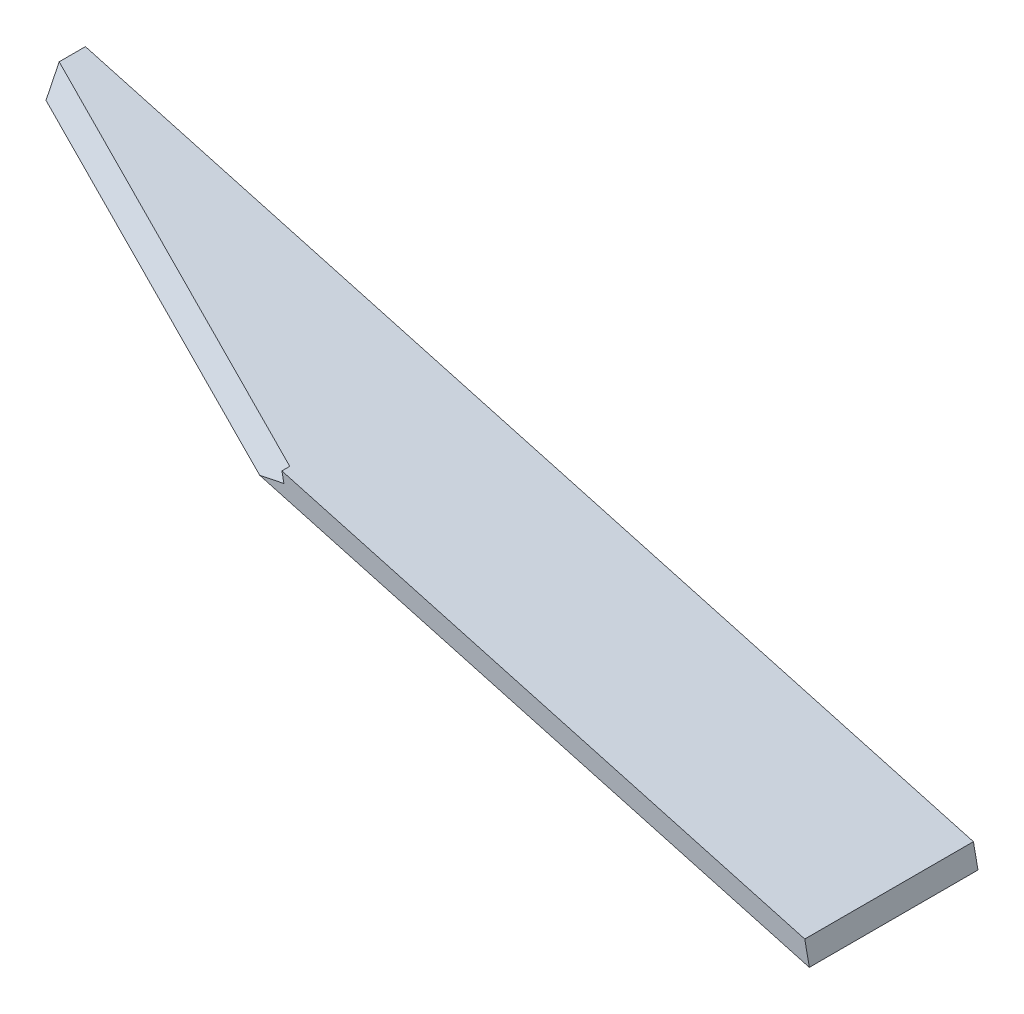
SolidWorks part; units mm, degrees
ref_plane "Front Plane" through (0, 0, 0) normal (0, 0, 1) x (1, 0, 0)
ref_plane "Top Plane" through (0, 0, 0) normal (0, 1, 0) x (1, 0, 0)
ref_plane "Right Plane" through (0, 0, 0) normal (1, 0, 0) x (0, 0, -1)
sketch "Sketch6" plane through (0, 0, 0) normal (0, 0, 1) x (1, 0, 0)
  line L0 (-76.7011, 15.8843) -> (-77.3811, 19.1832)
  line L1 (-76.7011, 15.8843) -> (-208.3286, 52.1284)
  line L2 (-77.3811, 19.1832) -> (-209.0086, 55.4273)
  line L3 (-208.3286, 52.1284) -> (-209.0086, 55.4273)
  line L4 (-208.3286, 52.1284) -> (-83.8661, 15.9709) construction
  line L5 (-81.2777, 18.2735) -> (-66.8847, -51.5513) construction
  line L7 (-97.2782, 105.8034) -> (-54.9066, -99.754) construction
  line L8 (-208.3286, 52.1284) -> (-83.8661, 15.9709) construction
  line L9 (-192.5333, -24.4993) -> (-172.8393, -120.0407) construction
  dimension "D1" = 3
extrude "Boss-Extrude3" add sketch "Sketch6" along normal blind 25
sketch "Sketch7" plane through (-7.7641, 37.6658, 49.2236) normal (-0.1243, 0.603, 0.788) x (0.9921, 0.0866, 0.0902)
  line L0 (-196.711, 7.3141) -> (-147.251, 14.6422)
  line L1 (-196.711, 7.3141) -> (-203.4139, 52.5544)
  line L2 (-147.251, 14.6422) -> (-153.9538, 59.8824)
  line L3 (-203.4139, 52.5544) -> (-153.9538, 59.8824)
  line L6 (41.5124, 88.8429) -> (-203.4139, 52.5544) construction
  line L7 (-189.6296, -40.4812) -> (-200.9149, 35.6873) construction
  dimension "D1" = 45.7341
  dimension "D2" = 50
extrude "Cut-Extrude1" cut sketch "Sketch7" along normal through all
